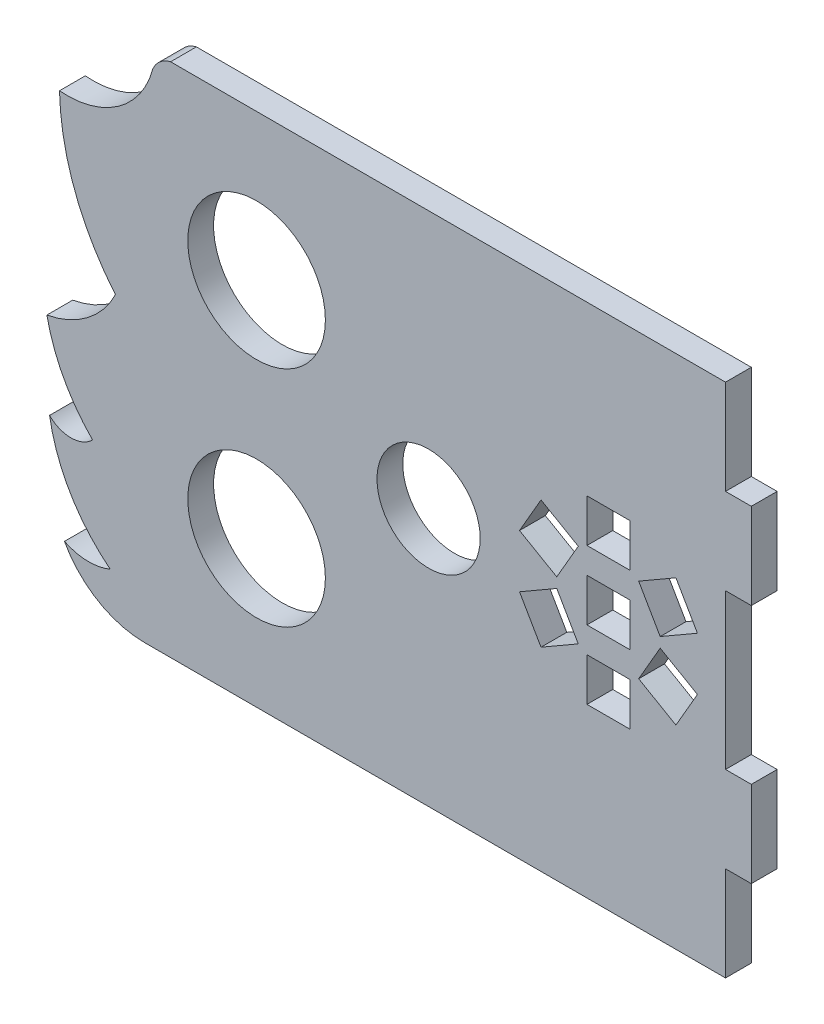
SolidWorks part; units mm, degrees
ref_plane "Alzado" through (0, 0, 0) normal (0, 0, 1) x (1, 0, 0)
ref_plane "Planta" through (0, 0, 0) normal (0, 1, 0) x (1, 0, 0)
ref_plane "Vista lateral" through (0, 0, 0) normal (1, 0, 0) x (0, 0, -1)
sketch "Model" plane through (0, 0, 0) normal (0, 0, 1) x (1, 0, 0)
  line L0 (81.0321, 50.1813) -> (81.0321, 60.1813)
  line L1 (81.0321, 60.1813) -> (78.0321, 60.1813)
  line L2 (78.0321, 60.1813) -> (78.0321, 71.1813)
  line L3 (78.0321, 71.1813) -> (66.9591, 71.1813)
  line L4 (66.9591, 71.1813) -> (56.2196, 71.1813)
  line L5 (56.2196, 71.1813) -> (47.2258, 71.1813)
  line L6 (47.2258, 71.1813) -> (42.1762, 71.1813)
  line L7 (42.1762, 71.1813) -> (32.3934, 71.1813)
  line L8 (32.3934, 71.1813) -> (26.9941, 71.1813)
  line L9 (26.9941, 71.1813) -> (16.9975, 71.1813)
  line L10 (16.9975, 71.1813) -> (13.507, 71.1813)
  line L11 (10.507, 11.1813) -> (21.6575, 11.1813)
  line L12 (21.6575, 11.1813) -> (43.7696, 11.1813)
  line L13 (43.7696, 11.1813) -> (66.512, 11.1813)
  line L14 (66.512, 11.1813) -> (78.0321, 11.1813)
  line L15 (78.0321, 11.1813) -> (78.0321, 22.1813)
  line L16 (78.0321, 22.1813) -> (81.0321, 22.1813)
  line L17 (81.0321, 22.1813) -> (81.0321, 32.1813)
  line L18 (81.0321, 32.1813) -> (78.0321, 32.1813)
  line L19 (78.0321, 32.1813) -> (78.0321, 50.1813)
  line L20 (78.0321, 50.1813) -> (81.0321, 50.1813)
  line L21 (61.923, 43.6813) -> (61.923, 38.6813)
  line L22 (61.923, 38.6813) -> (66.923, 38.6813)
  line L23 (66.923, 38.6813) -> (66.923, 43.6813)
  line L24 (66.923, 43.6813) -> (61.923, 43.6813)
  line L25 (61.923, 35.6813) -> (61.923, 30.6813)
  line L26 (61.923, 30.6813) -> (66.923, 30.6813)
  line L27 (66.923, 30.6813) -> (66.923, 35.6813)
  line L28 (66.923, 35.6813) -> (61.923, 35.6813)
  line L29 (72.2663, 48.5964) -> (67.9362, 46.0964)
  line L30 (67.9362, 46.0964) -> (70.4362, 41.7662)
  line L31 (70.4362, 41.7662) -> (74.7663, 44.2662)
  line L32 (74.7663, 44.2662) -> (72.2663, 48.5964)
  line L33 (67.9362, 36.2662) -> (72.2663, 33.7662)
  line L34 (72.2663, 33.7662) -> (74.7663, 38.0964)
  line L35 (74.7663, 38.0964) -> (70.4362, 40.5964)
  line L36 (70.4362, 40.5964) -> (67.9362, 36.2662)
  line L37 (61.923, 51.6813) -> (61.923, 46.6813)
  line L38 (61.923, 46.6813) -> (66.923, 46.6813)
  line L39 (66.923, 46.6813) -> (66.923, 51.6813)
  line L40 (66.923, 51.6813) -> (61.923, 51.6813)
  line L41 (56.5798, 33.7662) -> (60.9099, 36.2662)
  line L42 (60.9099, 36.2662) -> (58.4099, 40.5964)
  line L43 (58.4099, 40.5964) -> (54.0798, 38.0964)
  line L44 (54.0798, 38.0964) -> (56.5798, 33.7662)
  line L45 (60.9099, 46.0964) -> (56.5798, 48.5964)
  line L46 (56.5798, 48.5964) -> (54.0798, 44.2662)
  line L47 (54.0798, 44.2662) -> (58.4099, 41.7662)
  line L48 (58.4099, 41.7662) -> (60.9099, 46.0964)
  circle A0 centre (23.507, 54.1813) radius 8
  circle A1 centre (43.507, 41.1813) radius 6
  circle A2 centre (23.507, 28.1813) radius 8
  arc A3 (13.507, 71.1813) -> (11.4398, 69.4229) centre (14.207, 68.2641) ccw
  arc A4 (0.5891, 61.8041) -> (11.4398, 69.4229) centre (1.4787, 72.0734) ccw
  arc A5 (0.5891, 61.8041) -> (7.0969, 44.5235) centre (28.5125, 62.4542) ccw
  arc A6 (-0.8753, 38.4867) -> (7.0969, 44.5235) centre (-2.926, 49.4774) ccw
  arc A7 (-0.8753, 38.4867) -> (4.4346, 28.5611) centre (18.5193, 42.4792) ccw
  arc A8 (-0.5654, 28.5381) -> (4.4346, 28.5611) centre (1.9231, 31.0496) ccw
  arc A9 (-0.5654, 28.5381) -> (6.4899, 16.5705) centre (18.5201, 31.7261) ccw
  arc A10 (1.1672, 16.7175) -> (6.4899, 16.5705) centre (3.9928, 22.5925) ccw
  arc A11 (1.1672, 16.7175) -> (10.507, 11.1813) centre (10.5059, 21.826) ccw
extrude "Saliente-Extruir1" add sketch "Model" along normal blind 3
